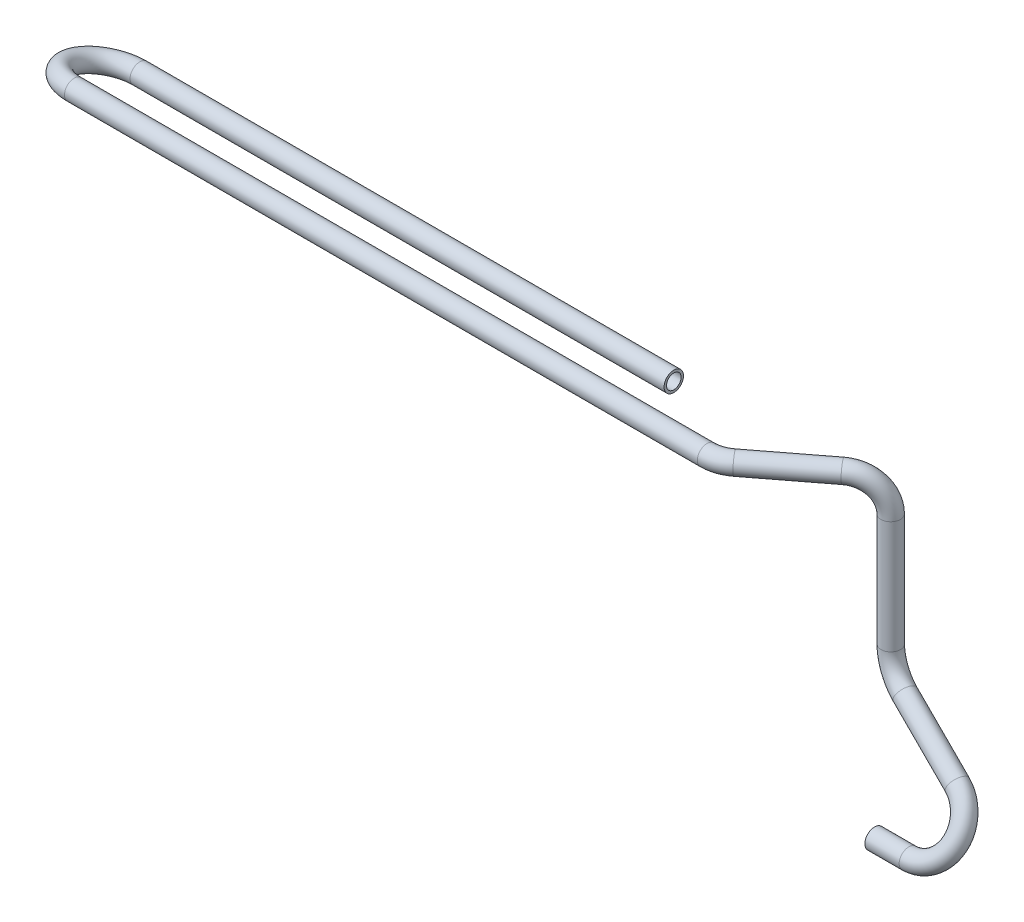
SolidWorks part; units mm, degrees
ref_plane "Plane1" through (0, 0, 0) normal (0, 0, 1) x (1, 0, 0)
ref_plane "Plane2" through (0, 0, 0) normal (0, 1, 0) x (1, 0, 0)
ref_plane "Plane3" through (0, 0, 0) normal (1, 0, 0) x (0, 0, -1)
sketch3d "3DSketch1"
  line L0 (0, 0, 0) -> (105, 0, 0) construction
  line L1 (105, 0, 0) -> (105, 0, -35) construction
  line L2 (105, 0, -35) -> (105, 60, -35) construction
  line L3 (0, 0, 0) -> (21.1375, 0, 0)
  line L4 (105, 60, -35) -> (-25, 60, -35) construction
  line L5 (-25, 60, -35) -> (-25, 164, -35) construction
  line L6 (-25, 164, -35) -> (-25.1, 164, -35) construction
  line L7 (-12.9889, 54.4564, -31.7662) -> (31.0342, 34.1381, -19.9139)
  line L8 (-25.0131, 73.6182, -35) -> (-25.0798, 143.016, -35)
  line L9 (-41.753, 164, -22.2327) -> (-79.4466, 164, 6.6657)
  line L10 (-25.1, 164, -35) -> (-25.1, 164, 11) construction
  line L11 (-25.1, 164, 11) -> (-85.1, 164, 11) construction
  line L12 (-92.2237, 164, 11) -> (-482.1, 164, 11)
  line L19 (-503.1, 152.5, -29.3949) -> (-503.1, 164, -29.3949) construction
  line L20 (-503.1, 164, -29.3949) -> (-503.1, 164, 11) construction
  line L22 (-153.1, 152.5, -29.3949) -> (-482.1, 152.5, -29.3949)
  line L23 (-503.1, 152.5, -29.3949) -> (-503.1, 164, 11) construction
  arc A0 (21.1375, 0, 0) -> (31.0342, 34.1381, -19.9139) centre (21.1375, 18.1394, -10.5813) ccw
  arc A1 (-41.753, 164, -22.2327) -> (-25.0798, 143.016, -35) centre (-41.7455, 143, -22.2229) ccw
  arc A2 (-12.9889, 54.4564, -31.7662) -> (-25.0131, 73.6182, -35) centre (-4.7358, 73.6377, -29.5383) ccw
  arc A3 (-92.2237, 164, 11) -> (-79.4466, 164, 6.6657) centre (-92.2237, 164, -10) ccw
  arc A4 (-482.1, 164, 11) -> (-482.1, 152.5, -29.3949) centre (-482.1, 158.25, -9.1975) ccw
  point P9 (105, 0, 0)
  point P12 (21.1375, 28.7206, 7.5581)
  point P16 (-25.1, 164, -35)
  point P18 (-54.5226, 142.9877, -38.8887)
  point P21 (-25, 60, -35)
  point P23 (0.7259, 73.643, -49.8156)
  point P28 (-85.1, 164, 11)
  point P30 (-92.2237, 185, -10)
  point P41 (-482.1, 138.0525, -3.4475)
  dimension "D4" = 130
  dimension "D6" = 0.1
  dimension "D7" = 21
  dimension "D8" = 21
  dimension "D9" = 21
  dimension "D13" = 21
  dimension "D16" = 478
  dimension "D17" = 350
  dimension "D14" = 21
  dimension "D1" = 105
  dimension "D2" = 60
  dimension "D3" = 35
  dimension "D5" = 104
  dimension "D10" = 46
  dimension "D11" = 60
  dimension "D15" = 11.5
ref_plane "Plane4" through (0, 0, 0) normal (1, 0, 0) x (0, 0, -1)
sketch "Sketch1" plane through (0, 0, 0) normal (1, 0, 0) x (0, 0, -1)
  circle A0 centre (0, 0) radius 6
  circle A1 centre (0, 0) radius 4.5
  dimension "D1" = 9
  dimension "D2" = 12
sweep "Sweep1" add profiles "Sketch1" path "3DSketch1"
